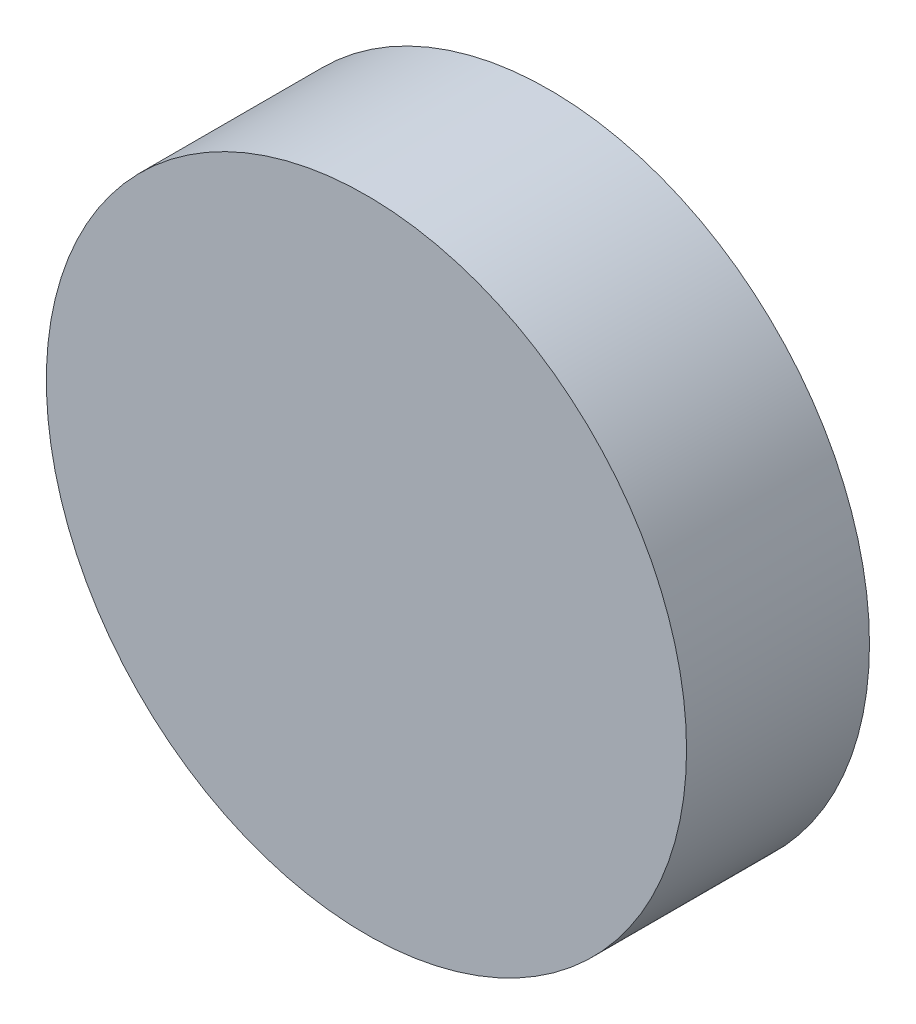
SolidWorks part; units mm, degrees
ref_plane "Front Plane" through (0, 0, 0) normal (0, 0, 1) x (1, 0, 0)
ref_plane "Top Plane" through (0, 0, 0) normal (0, 1, 0) x (1, 0, 0)
ref_plane "Right Plane" through (0, 0, 0) normal (1, 0, 0) x (0, 0, -1)
sketch "Sketch1" plane through (0, 0, 0) normal (0, 0, 1) x (1, 0, 0)
  circle A0 centre (0, 0) radius 1.75
  point P3 (0, 0)
  dimension "D1" = 3.5
extrude "Boss-Extrude1" add sketch "Sketch1" along normal blind 1
